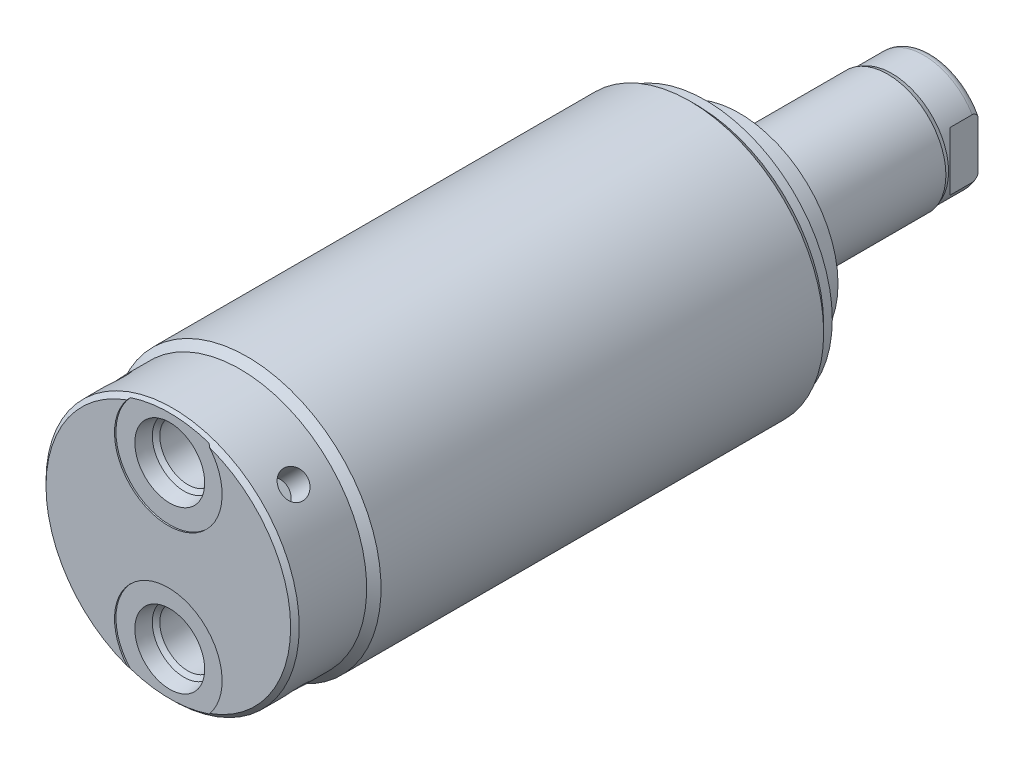
SolidWorks part; units mm, degrees
material "Alloy Steel"
ref_plane "Front Plane" through (0, 0, 0) normal (0, 0, 1) x (1, 0, 0)
ref_plane "Top Plane" through (0, 0, 0) normal (0, 1, 0) x (1, 0, 0)
ref_plane "Right Plane" through (0, 0, 0) normal (1, 0, 0) x (0, 0, -1)
ref_plane "Plane1" through (0, 0, 0) normal (0, 0, 1) x (1, 0, 0)
sketch "Sketch1" plane through (0, 0, 0) normal (0, 0, 1) x (1, 0, 0)
  circle A0 centre (0, 0) radius 23.6855
  dimension "D1" = 47.371
extrude "Extrude1" add sketch "Sketch1" along normal blind 95.123
sketch "Sketch2" plane through (0, 0, 0) normal (0, 1, 0) x (1, 0, 0)
  line L0 (23.6855, -95.123) -> (23.6855, -81.153)
  line L1 (23.6855, -81.153) -> (22.4155, -82.423)
  line L2 (22.4155, -82.423) -> (22.4155, -95.123)
  line L3 (22.4155, -95.123) -> (23.6855, -95.123)
  line L4 (0, 0) -> (0, -24.4965) construction
  line L5 (-23.6855, -95.123) -> (23.6855, -95.123) construction
  line L6 (23.6855, -95.123) -> (23.6855, 0) construction
  dimension "D1" = 12.7
  dimension "D2" = 44.831
  dimension "D3" = 45
revolve "Cut-Revolve1" cut sketch "Sketch2" angle 360 about L4
sketch "Sketch3" plane through (0, 0, 0) normal (0, 1, 0) x (1, 0, 0)
  line L0 (22.4155, 0) -> (22.4155, -1.524)
  line L1 (22.4155, -1.524) -> (23.6855, -2.794)
  line L2 (23.6855, -2.794) -> (23.6855, 0)
  line L3 (23.6855, 0) -> (22.4155, 0)
  line L4 (0, 0) -> (0, 3.0455) construction
  line L5 (22.4155, -95.123) -> (22.4155, -82.423) construction
  line L6 (23.6855, 0) -> (-23.6855, 0) construction
  line L7 (23.6855, -81.153) -> (23.6855, 0) construction
  dimension "D1" = 45
  dimension "D2" = 1.524
revolve "Cut-Revolve2" cut sketch "Sketch3" angle 360 about L4
chamfer "Chamfer1" distance 0.762 angle 45 1 edges at (-22.4155, 0, 95.123)
sketch "S2D0002" plane through (0, 0, 0) normal (1, 0, 0) x (0, -1, 0)
  line L0 (20.4597, -94.869) -> (23.7998, -94.869)
  line L1 (20.4597, -94.869) -> (19.9171, -92.3163)
  line L2 (19.9171, -92.3163) -> (19.2532, -91.6524)
  line L3 (19.2532, -91.6524) -> (19.2532, -80.899)
  line L4 (19.2532, -80.899) -> (14.2748, -80.899)
  line L5 (14.2748, -80.899) -> (14.2748, -95.123)
  line L6 (14.2748, -14.6685) -> (14.2748, 0.6985) construction
  line L8 (23.7998, -94.869) -> (23.7998, -95.123)
  line L9 (-22.4155, -95.123) -> (22.4155, -95.123) construction
  line L10 (23.7998, -95.123) -> (14.2748, -95.123)
  dimension "D1" = 19.05
  dimension "D2" = 9.9568
  dimension "D3" = 0.254
  dimension "D4" = 12.3698
  dimension "D5" = 12
  dimension "D6" = 45
  dimension "D7" = 2.5527
  dimension "D8" = 13.97
  dimension "D9" = 14.2748
revolve "Cut-Revolve3" cut sketch "S2D0002" angle 360 about L6
sketch "Sketch6" plane through (0, 0, 0) normal (0, 0, -1) x (-1, 0, 0)
  circle A0 centre (0, 0) radius 17.4625
  circle A1 centre (0, 0) radius 23.6855 construction
  dimension "D1" = 34.925
extrude "Extrude2" add sketch "Sketch6" along normal blind 5.969
sketch "Sketch7" plane through (0, 0, 0) normal (1, 0, 0) x (0, 0, -1)
  line L0 (5.969, 0) -> (5.969, -10.3187)
  line L1 (5.969, -10.3187) -> (39.624, -10.3187)
  line L2 (39.624, -10.3187) -> (39.624, 0)
  line L3 (39.624, 0) -> (5.969, 0)
  line L4 (0, 0) -> (9.7123, 0) construction
  line L5 (5.969, -17.4625) -> (5.969, 17.4625) construction
  dimension "D1" = 20.6375
  dimension "D2" = 33.655
revolve "Revolve1" add sketch "Sketch7" angle 360 about L4
sketch "S2D0001" plane through (0, 0, 0) normal (0, 1, 0) x (1, 0, 0)
  line L0 (3.2639, 37.6883) -> (3.2639, 24.5618)
  line L1 (3.2639, 24.5618) -> (0, 24.5618)
  line L2 (4.3815, 39.624) -> (0, 39.624)
  line L3 (0, 39.624) -> (0, 24.5618)
  line L4 (3.2639, 37.6883) -> (4.3815, 39.624)
  line L5 (0, -31.3084) -> (0, 2.765) construction
  line L6 (10.3188, 39.624) -> (-10.3188, 39.624) construction
  dimension "D1" = 8.763
  dimension "D2" = 30
  dimension "D3" = 15.0622
  dimension "D4" = 6.5278
revolve "Cut-Revolve5" cut sketch "S2D0001" angle 360 about L5
ref_plane "Plane8" through (0, 0, 0) normal (1, 0, 0) x (0, -1, 0)
sketch "Sketch9" plane through (0, 0, 0) normal (1, 0, 0) x (0, -1, 0)
  line L0 (-10.3188, 32.2072) -> (-10.033, 32.9692)
  line L1 (-10.033, 32.9692) -> (-10.033, 38.608)
  line L2 (0, 12.6594) -> (0, 20.8178) construction
  line L3 (10.3187, 39.624) -> (-10.3188, 39.624) construction
  line L4 (-9.6449, 39.624) -> (-10.3188, 39.624)
  line L5 (-10.3188, 39.624) -> (-10.3188, 32.2072)
  arc A0 (-9.6449, 39.624) -> (-10.033, 38.608) centre (-8.509, 38.608) ccw
  dimension "D1" = 1.524
  dimension "D2" = 1.016
  dimension "D3" = 20.066
  dimension "D4" = 0.762
  dimension "D5" = 7.4168
revolve "Cut-Revolve6" cut sketch "Sketch9" angle 360 about L2
sketch "Sketch13" plane through (0, 0, 0) normal (0, 1, 0) x (1, 0, 0)
  line L0 (8.5852, 39.624) -> (8.5852, 34.671)
  line L1 (8.5852, 34.671) -> (10.033, 33.2232)
  line L2 (-8.5852, 39.624) -> (-8.5852, 34.671)
  line L3 (-8.5852, 34.671) -> (-10.033, 33.2232)
  line L4 (9.6449, 39.624) -> (-9.6449, 39.624) construction
  line L5 (0, 13.7262) -> (0, 20.767) construction
  line L6 (10.033, 33.2232) -> (10.033, 39.624)
  line L8 (8.5852, 39.624) -> (10.033, 39.624)
  line L9 (10.033, 32.9692) -> (10.033, 38.608) construction
  line L10 (-10.033, 33.2232) -> (-10.033, 39.624)
  line L11 (-8.5852, 39.624) -> (-10.033, 39.624)
  dimension "D1" = 17.1704
  dimension "D2" = 135
  dimension "D3" = 4.953
extrude "Cut-Extrude4" cut sketch "Sketch13" against normal mid plane 39.685
ref_plane "Plane13" through (0, 0, 0) normal (0.7071, 0.7071, 0) x (0, 0, -1)
hole_wizard "Hole1" positions "3DSketch2" profile "Sketch14" legacy
sketch3d "3DSketch2"
  point P0 (-15.8502, 15.8502, 88.773)
  dimension "D1" = 6.35
sketch "Sketch14" plane through (-15.8502, 15.8502, 88.773) normal (0, 0, 1) x (-0.7071, -0.7071, 0)
  line L0 (0, 0) -> (0, 4.7498)
  line L1 (0, 4.7498) -> (2.3749, 4.7498)
  line L2 (2.3749, 4.7498) -> (2.3749, 0)
  line L3 (2.3749, 0) -> (0, 0)
  line L4 (0, 110) -> (0, -10) construction
  dimension "Diameter" = 4.7498
  dimension "Depth" = 4.7498
pattern_circular "CirPattern1" count 4 over 360 about axis through (0, 0, 0) along (0, 0, 1) of "Hole1"
pattern_linear "LPattern1" count 2 spacing 28.5496 along (0, 1, 0) of "Cut-Revolve3"
